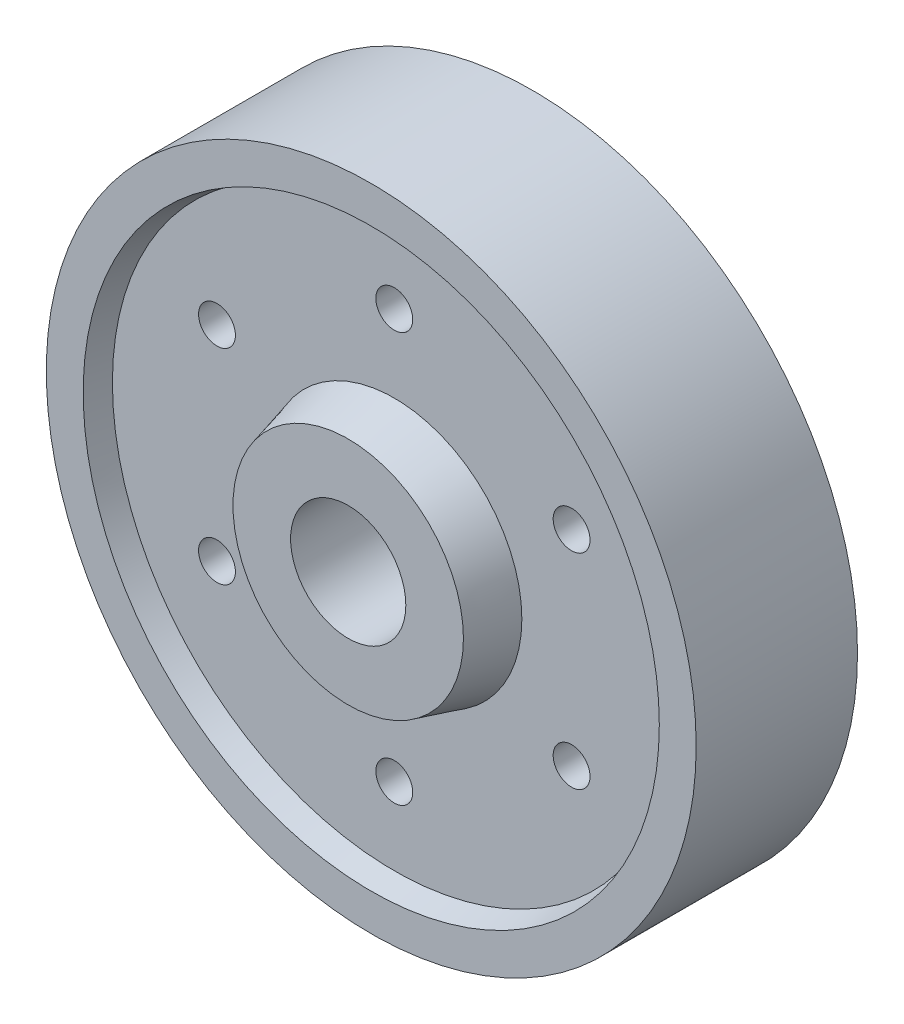
SolidWorks part; units mm, degrees
material "1060 Alloy"
ref_plane "Front Plane" through (0, 0, 0) normal (0, 0, 1) x (1, 0, 0)
ref_plane "Top Plane" through (0, 0, 0) normal (0, 1, 0) x (1, 0, 0)
ref_plane "Right Plane" through (0, 0, 0) normal (1, 0, 0) x (0, 0, -1)
sketch "Sketch8" plane through (0, 0, 0) normal (1, 0, 0) x (0, 0, -1)
  line L0 (-62.2655, 0) -> (70.3981, 0) construction
  line L1 (0, 90.0915) -> (0, -29.6439) construction
  line L2 (22.5, 12.5) -> (-22.5, 12.5)
  line L3 (-22.5, 12.5) -> (-22.5, 25)
  line L4 (-22.5, 25) -> (-12.5, 27.6795)
  line L5 (-12.5, 27.6795) -> (-12.5, 61.1603)
  line L6 (-12.5, 61.1603) -> (-17.5, 62.5)
  line L7 (-17.5, 62.5) -> (-17.5, 70.5)
  line L8 (-17.5, 70.5) -> (17.5, 70.5)
  line L9 (62.2655, 0) -> (-70.3981, 0) construction
  line L10 (17.5, 62.5) -> (17.5, 70.5)
  line L11 (12.5, 61.1603) -> (17.5, 62.5)
  line L12 (12.5, 27.6795) -> (12.5, 61.1603)
  line L13 (22.5, 25) -> (12.5, 27.6795)
  line L14 (22.5, 12.5) -> (22.5, 25)
  point P16 (0, 70.5)
  point P21 (0, 12.5)
  dimension "D1" = 15
  dimension "D2" = 15
  dimension "D3" = 22.5
  dimension "D4" = 12.5
  dimension "D5" = 5
  dimension "D6" = 10
  dimension "D7" = 58
  dimension "D8" = 8
  dimension "D9" = 12.5
  dimension "D10" = 0
  dimension "D11" = 0
revolve "Revolve3" add sketch "Sketch8" angle 360 about L0
sketch "Sketch9" plane through (0, 0, 12.5) normal (0, 0, 1) x (1, 0, 0)
  line L0 (0, 27.6795) -> (0, 61.1603) construction
  circle A0 centre (0, 0) radius 27.6795 construction
  circle A1 centre (0, 0) radius 61.1603 construction
  circle A2 centre (0, 44.4199) radius 4
  circle A3 centre (38.4687, 22.2099) radius 4
  circle A4 centre (38.4687, -22.2099) radius 4
  circle A5 centre (0, -44.4199) radius 4
  circle A6 centre (-38.4687, -22.2099) radius 4
  circle A7 centre (-38.4687, 22.2099) radius 4
  point P22 (0, 0)
  dimension "D1" = 8
  dimension "D2" = 6
extrude "Cut-Extrude2" cut sketch "Sketch9" against normal up to next
